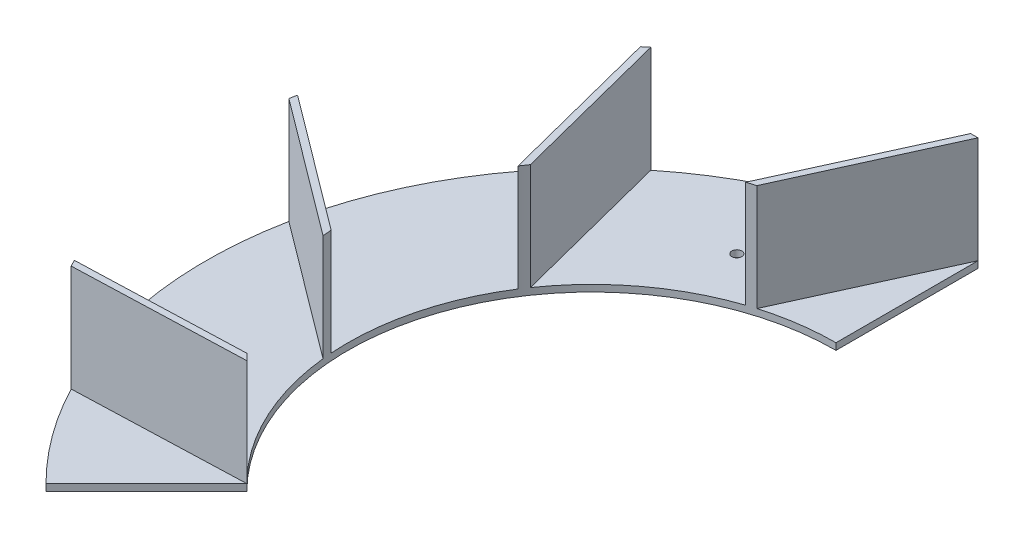
SolidWorks part; units mm, degrees
ref_plane "Front Plane" through (0, 0, 0) normal (0, 0, 1) x (1, 0, 0)
ref_plane "Top Plane" through (0, 0, 0) normal (0, 1, 0) x (1, 0, 0)
ref_plane "Right Plane" through (0, 0, 0) normal (1, 0, 0) x (0, 0, -1)
sketch "Sketch1" plane through (0, 0, 0) normal (0, 1, 0) x (1, 0, 0)
  line L2 (0, 110) -> (0, 174)
  line L3 (-123.0366, -123.0366) -> (-77.7817, -77.7817)
  arc A0 (0, 110) -> (-77.7817, -77.7817) centre (0, 0) ccw
  arc A2 (0, 174) -> (-123.0366, -123.0366) centre (0, 0) ccw
  dimension "D1" = 174
  dimension "D2" = 110
extrude "Boss-Extrude3" add sketch "Sketch1" along normal blind 3
sketch "Sketch2" plane through (0, 3, 0) normal (0, 1, 0) x (1, 0, 0)
  line L0 (0, 174) -> (-31.1541, 105.4961)
  line L1 (-31.1541, 105.4961) -> (-35.0015, 104.2827) construction
  line L2 (-35.0015, 104.2827) -> (-3.31, 173.9685)
  line L3 (-3.31, 173.9685) -> (0, 174) construction
  line L4 (0, 110) -> (0, 174) construction
  line L5 (-15.577, 139.748) -> (-18.3079, 140.99) construction
  line L6 (-109.0655, 135.5755) -> (-90.4006, 62.6716)
  line L7 (-92.6379, 59.3145) -> (-111.6248, 133.4763)
  line L8 (-169.961, 37.2727) -> (-109.7208, -7.8325)
  line L9 (-109.3598, -11.8506) -> (-170.6393, 34.0328)
  line L10 (-155.7915, -77.492) -> (-80.5816, -74.8773)
  line L11 (-77.7817, -77.7817) -> (-154.2892, -80.4416)
  arc A0 (0, 174) -> (-123.0366, -123.0366) centre (0, 0) ccw construction
  arc A1 (0, 110) -> (-77.7817, -77.7817) centre (0, 0) ccw construction
  arc A2 (-31.1541, 105.4961) -> (-35.0015, 104.2827) centre (0, 0) ccw
  arc A3 (0, 174) -> (-3.31, 173.9685) centre (0, 0) ccw
  arc A4 (-109.0655, 135.5755) -> (-111.6248, 133.4763) centre (0, 0) ccw
  arc A5 (-90.4006, 62.6716) -> (-92.6379, 59.3145) centre (0, 0) ccw
  arc A6 (-169.961, 37.2727) -> (-170.6393, 34.0328) centre (0, 0) ccw
  arc A7 (-109.7208, -7.8325) -> (-109.3598, -11.8506) centre (0, 0) ccw
  arc A8 (-155.7915, -77.492) -> (-154.2892, -80.4416) centre (0, 0) ccw
  arc A9 (-80.5816, -74.8773) -> (-77.7817, -77.7817) centre (0, 0) ccw
  dimension "D1" = 3
  dimension "D2" = 65
  dimension "D3" = 4
extrude "Boss-Extrude4" add sketch "Sketch2" along normal blind 48
sketch "Sketch3" plane through (0, 0, 0) normal (0, -1, 0) x (1, 0, 0)
  line L0 (-57.0535, -122.3516) -> (0, 0) construction
  line L1 (0, 0) -> (-130.4, 34.9406) construction
  circle A0 centre (-57.0535, -122.3516) radius 2.25
  circle A1 centre (-130.4, 34.9406) radius 2.25
  point P10 (0, -110)
  dimension "D1" = 4.5
  dimension "D2" = 80
  dimension "D3" = 135
  dimension "D4" = 25
extrude "Cut-Extrude1" cut sketch "Sketch3" against normal up to next
